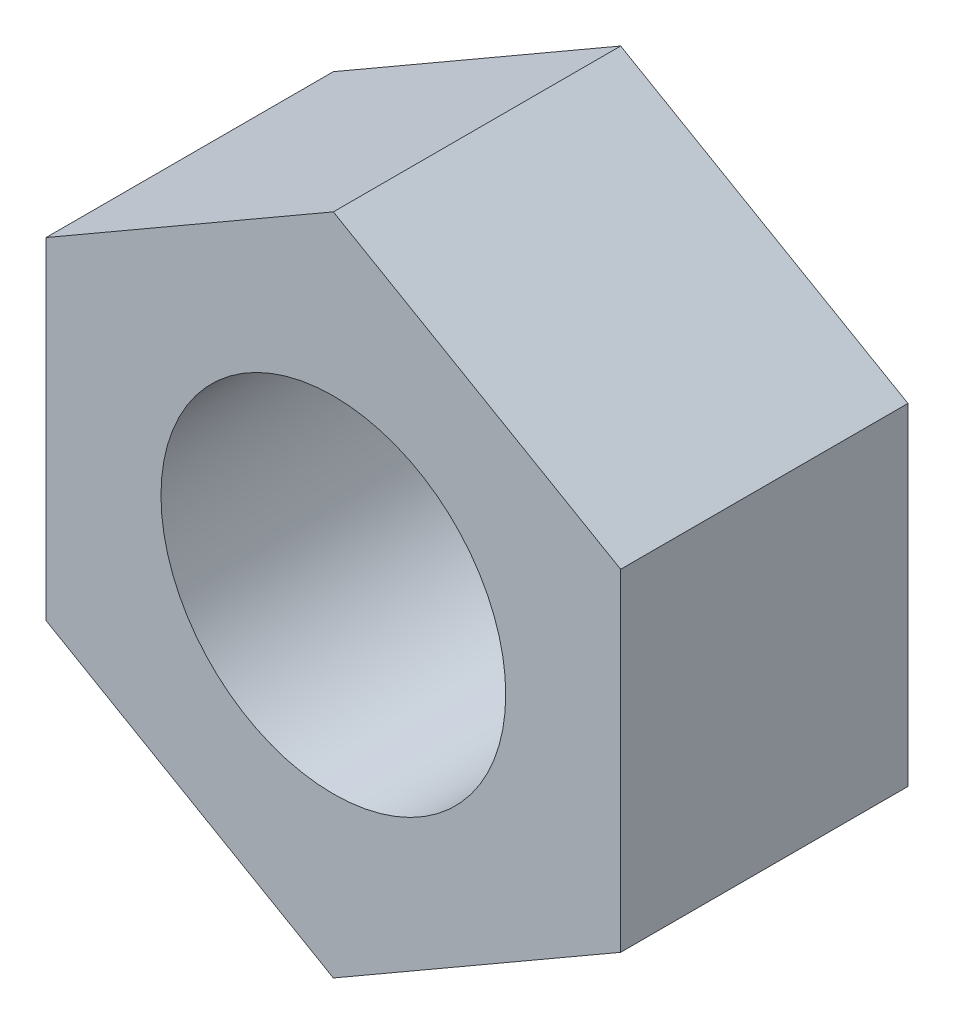
SolidWorks part; units mm, degrees
ref_plane "Front Plane" through (0, 0, 0) normal (0, 0, 1) x (1, 0, 0)
ref_plane "Top Plane" through (0, 0, 0) normal (0, 1, 0) x (1, 0, 0)
ref_plane "Right Plane" through (0, 0, 0) normal (1, 0, 0) x (0, 0, -1)
sketch "Sketch1" plane through (0, 0, 0) normal (0, 0, 1) x (1, 0, 0)
  line L1 (5, -2.8868) -> (5, 2.8868)
  line L2 (5, 2.8868) -> (0, 5.7735)
  line L3 (0, 5.7735) -> (-5, 2.8868)
  line L4 (-5, 2.8868) -> (-5, -2.8868)
  line L5 (-5, -2.8868) -> (0, -5.7735)
  line L6 (0, -5.7735) -> (5, -2.8868)
  circle A0 centre (0, 0) radius 5 construction
  circle A1 centre (0, 0) radius 3
  dimension "D1" = 10
  dimension "D2" = 6
extrude "Boss-Extrude1" add sketch "Sketch1" along normal blind 5
